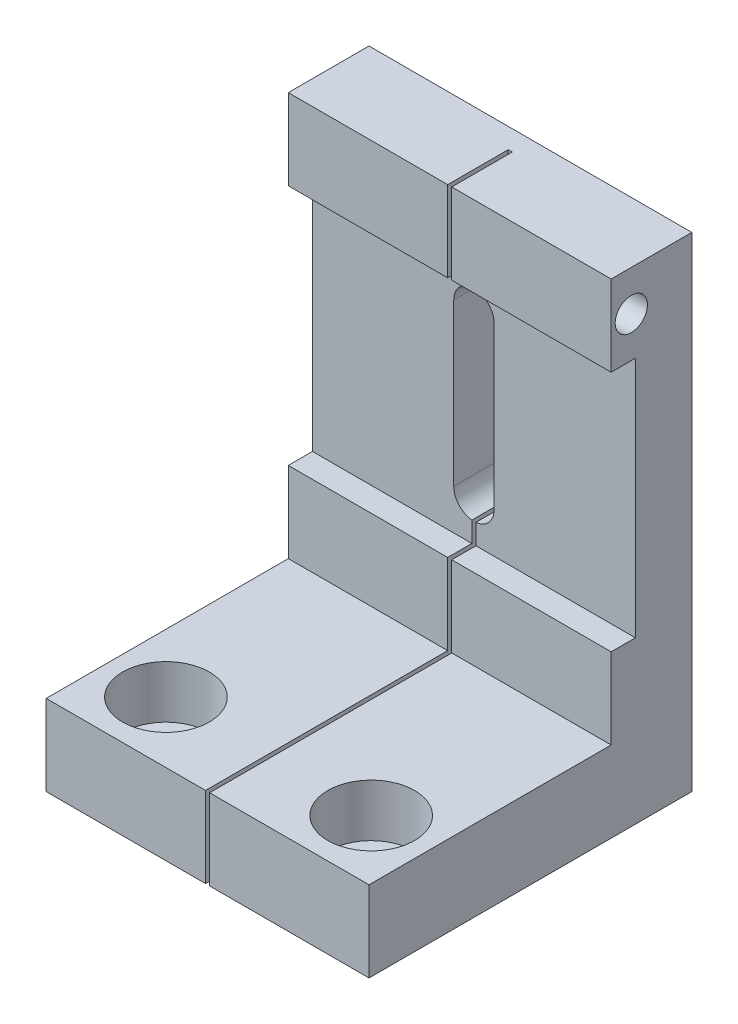
SolidWorks part; units mm, degrees
ref_plane "Front Plane" through (0, 0, 0) normal (0, 0, 1) x (1, 0, 0)
ref_plane "Top Plane" through (0, 0, 0) normal (0, 1, 0) x (1, 0, 0)
ref_plane "Right Plane" through (0, 0, 0) normal (1, 0, 0) x (0, 0, -1)
sketch "Sketch1" plane through (0, 0, 0) normal (0, 0, 1) x (1, 0, 0)
  line L1 (0, 0) -> (-40, 0)
  line L2 (0, 0) -> (0, -60)
  line L3 (0, -60) -> (-40, -60)
  line L4 (-40, 0) -> (-40, -60)
  dimension "D1" = 40
  dimension "D2" = 60
extrude "Boss-Extrude1" add sketch "Sketch1" along normal blind 10
sketch "Sketch2" plane through (0, 0, 10) normal (0, 0, 1) x (1, 0, 0)
  line L0 (-20, -15) -> (-20, -35) construction
  line L1 (-17.5, -15) -> (-17.5, -35)
  line L2 (-22.5, -15) -> (-22.5, -35)
  line L4 (-40, -60) -> (0, -60) construction
  line L5 (0, 0) -> (-40, 0) construction
  line L6 (-20, 0) -> (-20, -5.6142) construction
  arc A0 (-17.5, -15) -> (-22.5, -15) centre (-20, -15) ccw
  arc A1 (-22.5, -35) -> (-17.5, -35) centre (-20, -35) ccw
  point P2 (-20, -25)
  dimension "D1" = 5
  dimension "D2" = 20
  dimension "D4" = 35
extrude "Cut-Extrude1" cut sketch "Sketch2" against normal through all
sketch "Sketch5" plane through (0, 0, 0) normal (1, 0, 0) x (0, 0, -1)
  line L0 (-7, -10) -> (-10, -10)
  line L1 (-10, -60) -> (-10, 0) construction
  line L2 (-7, -10) -> (-7, -40)
  line L3 (-10, -60) -> (0, -60) construction
  line L4 (-7, -40) -> (-10, -40)
  line L7 (-10, -10) -> (-10, -40)
  dimension "D1" = 3
  dimension "D4" = 30
  dimension "D5" = 20
extrude "Cut-Extrude4" cut sketch "Sketch5" against normal through all
sketch "Sketch6" plane through (0, 0, 10) normal (0, 0, 1) x (1, 0, 0)
  line L0 (-40, -40) -> (-40, -60) construction
  line L1 (0, -60) -> (-40, -60)
  line L2 (0, -60) -> (0, -50)
  line L3 (0, -50) -> (-40, -50)
  line L4 (-40, -60) -> (-40, -50)
  dimension "D1" = 10
extrude "Boss-Extrude2" add sketch "Sketch6" along normal blind 30
sketch "Sketch7" plane through (0, -50, 0) normal (0, 1, 0) x (1, 0, 0)
  line L3 (-40, -40) -> (-40, -10) construction
  circle A0 centre (-4.0875, -15.1829) radius 2
  circle A1 centre (-35.875, -15.1829) radius 2
  dimension "D1" = 4
  dimension "D2" = 4
  dimension "D3" = 4.125
  dimension "D5" = 31.7875
extrude "Cut-Extrude5" [suppressed] cut sketch "Sketch7" against normal blind 40
sketch "Sketch8" plane through (0, 0, 0) normal (0, 1, 0) x (1, 0, 0)
  line L0 (0, -10) -> (-40, -10) construction
  line L1 (-22.5, -4.1376) -> (-17.5, -4.1376) construction
  line L2 (-20.25, -40) -> (-19.75, -40)
  line L4 (-17.5, 0) -> (-17.5, -7) construction
  line L5 (-20.25, -40) -> (-20.25, -2.5)
  line L6 (-20, -4.1376) -> (-20, -0.8167) construction
  line L7 (0, -40) -> (-40, -40) construction
  line L8 (-20, -2.5) -> (-20, -2.3025) construction
  line L9 (-20.25, -2.5) -> (-19.75, -2.5)
  line L10 (-19.75, -40) -> (-19.75, -2.5)
  line L11 (-22.5, 0) -> (-22.5, -7) construction
  dimension "D1" = 0.5
  dimension "D3" = 7.5
extrude "Cut-Extrude7" cut sketch "Sketch8" against normal up to surface (60 mm away) up to face at (-20, -60, 20)
sketch "Sketch9" plane through (0, -60, 0) normal (0, -1, 0) x (1, 0, 0)
  line L3 (0, 40) -> (0, 0) construction
  line L5 (-40, 7) -> (-20.25, 7) construction
  circle A0 centre (-32.73, 5) radius 2
  circle A1 centre (-7.3, 5) radius 2
  dimension "D1" = 4
  dimension "D3" = 7.3
  dimension "D4" = 4
  dimension "D2" = 25.43
extrude "Cut-Extrude9" [suppressed] cut sketch "Sketch9" against normal blind 15
sketch "Sketch10" plane through (0, 0, 0) normal (1, 0, 0) x (0, 0, -1)
  line L1 (-10, 0) -> (0, 0) construction
  line L2 (-10, -10) -> (-10, 0) construction
  circle A0 centre (-7.5, -5) radius 2
  dimension "D1" = 4
  dimension "D2" = 5
  dimension "D3" = 2.5
extrude "Cut-Extrude10" cut sketch "Sketch10" against normal blind 30
sketch "Sketch12" plane through (0, -60, 0) normal (0, -1, 0) x (1, 0, 0)
  line L0 (-32.73, 32.43) -> (-32.73, 7) construction
  line L1 (-32.73, 7) -> (-7.3, 7) construction
  line L2 (-7.3, 7) -> (-7.3, 32.43) construction
  line L3 (-7.3, 32.43) -> (-32.73, 32.43) construction
  line L5 (-40, 7) -> (-20.25, 7) construction
  line L6 (0, 40) -> (0, 0) construction
  line L10 (-19.75, 40) -> (0, 40) construction
  line L11 (-40, 0) -> (-40, 40) construction
  circle A0 centre (-7.3, 32.43) radius 3.4
  circle A1 centre (-32.73, 32.43) radius 3.4
  circle A2 centre (-32.73, 7) radius 2.49
  circle A3 centre (-7.3, 7) radius 2.49
  circle A4 centre (-7.3, 32.43) radius 5.375 construction
  circle A5 centre (-32.73, 7.03) radius 3.4 [skipped]
  circle A6 centre (-7.3, 7.03) radius 3.4 [skipped]
  dimension "D1" = 6.8
  dimension "D2" = 2
  dimension "D3" = 2
  dimension "D4" = 10.75
  dimension "D6" = 7.3
  dimension "D7" = 25.43
  dimension "D8" = 4.98
  dimension "D9" = 25.43
  dimension "D11" = 7.57
  dimension "D5" = 2
  dimension "D12" = 7.27
extrude "Cut-Extrude13" cut sketch "Sketch12" against normal up to surface (10 mm away) up to face at (-9.875, -50, 25)
sketch "Sketch14" plane through (0, -50, 0) normal (0, 1, 0) x (1, 0, 0)
  line L0 (-32.73, -32.43) -> (18.13, -32.43) construction
  circle A0 centre (-32.73, -32.43) radius 5.375
  circle A1 centre (-7.3, -32.43) radius 5.375
  dimension "D1" = 10.75
  dimension "D3" = 25.43
  dimension "D2" = 2
extrude "Cut-Extrude14" cut sketch "Sketch14" against normal blind 6.5
sketch "Sketch16" plane through (0, 0, 0) normal (0, 0, -1) x (-1, 0, 0)
  line L0 (20, -12.5) -> (20, -37.5) construction
  line L1 (20, -25) -> (20.9851, -25) construction
  arc A0 (22.5, -15) -> (17.5, -15) centre (20, -15) ccw construction
  arc A1 (17.5, -35) -> (22.5, -35) centre (20, -35) ccw construction
ref_plane "Plane1" through (-20, 0, 0) normal (-1, 0, 0) x (0, 0, 1)
sketch "Sketch17" plane through (-20, 0, 0) normal (-1, 0, 0) x (0, 0, 1)
  line L0 (0, -25) -> (28.7273, -25) construction
equation "\"inch\"= 25.43"
equation "\"D5@Sketch7\"=\"inch\"*1.25"
equation "\"D2@Sketch9\"=\"inch\""
equation "\"D7@Sketch12\"=\"inch\""
equation "\"D3@Sketch14\" = \"inch\""
equation "\"D9@Sketch12\"=\"inch\""
